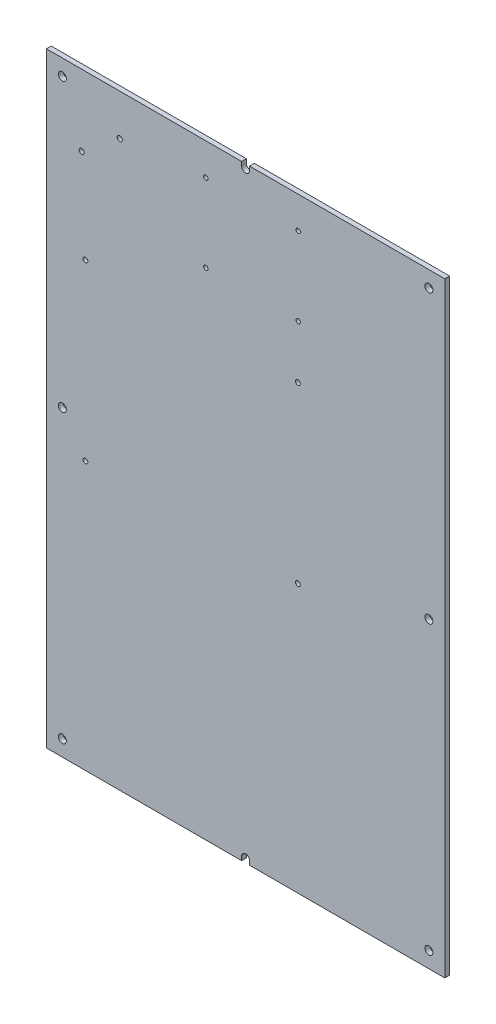
SolidWorks part; units mm, degrees
ref_plane "Plan de face" through (0, 0, 0) normal (0, 0, 1) x (1, 0, 0)
ref_plane "Plan de dessus" through (0, 0, 0) normal (0, 1, 0) x (1, 0, 0)
ref_plane "Plan de droite" through (0, 0, 0) normal (1, 0, 0) x (0, 0, -1)
sketch "Esquisse1" plane through (0, 0, 0) normal (0, 0, 1) x (1, 0, 0)
  line L0 (92.3378, -311.3528) -> (92.3378, -313.8528)
  line L1 (87.3378, 66.1472) -> (-35.1622, 66.1472)
  line L2 (214.8378, 66.1472) -> (214.8378, -313.8528)
  line L3 (87.3378, -313.8528) -> (-35.1622, -313.8528)
  line L4 (-35.1622, 66.1472) -> (-35.1622, -313.8528)
  line L5 (87.3378, -311.3528) -> (87.3378, -313.8528)
  line L6 (92.3378, -313.8528) -> (214.8378, -313.8528)
  line L7 (92.3378, 63.6472) -> (92.3378, 66.1472)
  line L8 (87.3378, 63.6472) -> (87.3378, 66.1472)
  line L9 (92.3378, 66.1472) -> (214.8378, 66.1472)
  line L10 (-35.1622, -123.8528) -> (214.8378, -123.8528) construction
  line L11 (61.3378, 49.6472) -> (146.3378, 49.6472) construction
  line L12 (146.3378, 49.6472) -> (146.3378, -6.3528) construction
  line L13 (146.3378, -6.3528) -> (61.3378, -6.3528) construction
  line L14 (61.3378, -6.3528) -> (61.3378, 49.6472) construction
  line L15 (119.6266, -38.8928) -> (68.049, -38.8928) construction
  line L16 (68.049, -38.8928) -> (68.049, -44.6928) construction
  line L17 (68.049, -44.6928) -> (119.6266, -44.6928) construction
  line L18 (119.6266, -44.6928) -> (119.6266, -38.8928) construction
  line L19 (93.8378, -38.8928) -> (93.8378, -44.6928) construction
  line L20 (89.8378, 63.6472) -> (89.8378, -311.3528) construction
  line L21 (64.8378, 46.1472) -> (122.8378, 46.1472) construction
  line L22 (93.8378, 46.1472) -> (93.8378, 49.6472) construction
  line L24 (-15.691, 43.1189) -> (14.659, 43.1189) construction
  line L25 (-15.691, 43.1189) -> (-15.691, 18.9889) construction
  line L26 (-15.691, 18.9889) -> (14.659, 18.9889) construction
  line L27 (14.659, 43.1189) -> (14.659, 18.9889) construction
  arc A0 (87.3378, 63.6472) -> (92.3378, 63.6472) centre (89.8378, 63.6472) ccw
  arc A1 (87.3378, -311.3528) -> (92.3378, -311.3528) centre (89.8378, -311.3528) cw
  circle A2 centre (64.8378, 46.1472) radius 1.375
  circle A3 centre (122.8378, 46.1472) radius 1.375
  circle A4 centre (64.8378, -2.8528) radius 1.375
  circle A5 centre (122.8378, -2.8528) radius 1.375
  circle A6 centre (-10.691, -36.3528) radius 1.5
  circle A7 centre (122.659, -36.3528) radius 1.5
  circle A8 centre (122.659, -145.5728) radius 1.5
  circle A9 centre (-10.691, -145.5728) radius 1.5
  circle A10 centre (-25.1622, 56.1472) radius 2.5
  circle A11 centre (204.8378, 56.1472) radius 2.5
  circle A12 centre (204.8378, -303.8528) radius 2.5
  circle A13 centre (-25.1622, -303.8528) radius 2.5
  circle A14 centre (204.8378, -123.8528) radius 2.5
  circle A15 centre (-25.1622, -123.8528) radius 2.5
  circle A16 centre (10.849, 40.3289) radius 1.6
  circle A17 centre (-13.021, 21.4889) radius 1.6
  point P66 (-50.4394, 55.8176)
  dimension "D3" = 375
  dimension "D6" = 190
  dimension "D7" = 2.75
  dimension "D8" = 2.75
  dimension "D10" = 2.75
  dimension "D14" = 2.75
  dimension "D21" = 3
  dimension "D22" = 3
  dimension "D23" = 3
  dimension "D24" = 3
  dimension "D37" = 5
  dimension "D40" = 5
  dimension "D42" = 24.13
  dimension "D45" = 3.2
  dimension "D48" = 3.2
  dimension "D1" = 250
  dimension "D2" = 190
  dimension "D4" = 190
  dimension "D5" = 190
  dimension "D9" = 58
  dimension "D11" = 49
  dimension "D12" = 20
  dimension "D13" = 100
  dimension "D15" = 49
  dimension "D16" = 58
  dimension "D17" = 3.5
  dimension "D18" = 3.5
  dimension "D19" = 3.5
  dimension "D20" = 85
  dimension "D25" = 109.22
  dimension "D26" = 30
  dimension "D27" = 133.35
  dimension "D28" = 109.22
  dimension "D29" = 133.35
  dimension "D30" = 2.54
  dimension "D31" = 109.22
  dimension "D32" = 5.8
  dimension "D33" = 78.74
  dimension "D34" = 0
  dimension "D35" = 25.7888
  dimension "D36" = 122.5
  dimension "D38" = 10
  dimension "D39" = 10
  dimension "D41" = 10
  dimension "D43" = 30.35
  dimension "D44" = 5
  dimension "D46" = 2.79
  dimension "D47" = 3.81
  dimension "D49" = 2.67
  dimension "D50" = 2.5
extrude "Boss.-Extru.1" add sketch "Esquisse1" along normal blind 3
